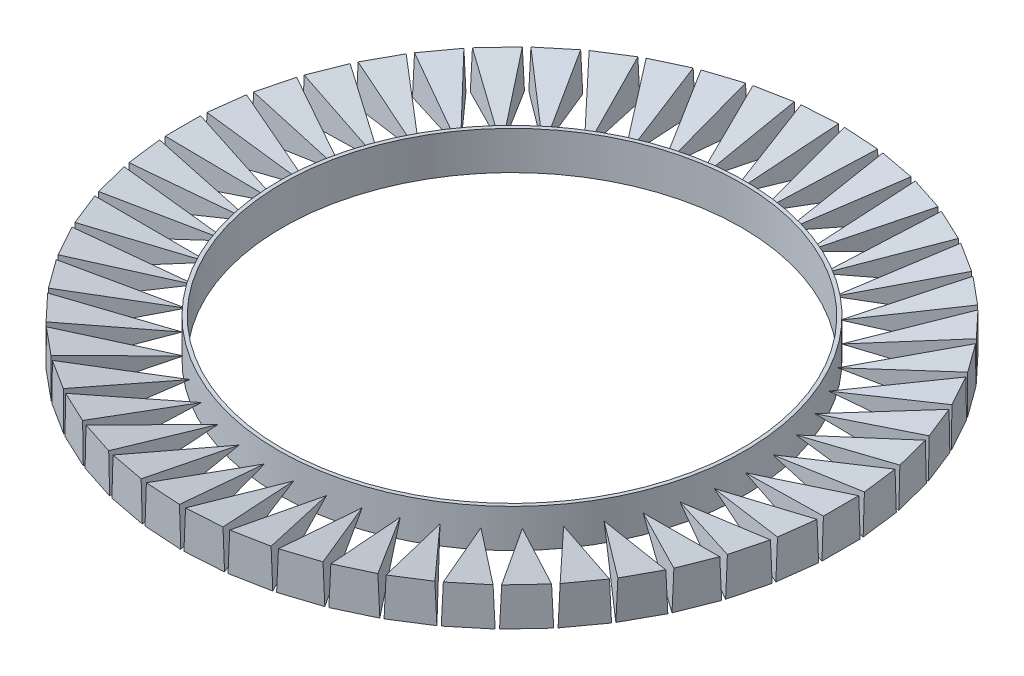
SolidWorks part; units mm, degrees
ref_plane "Front Plane" through (0, 0, 0) normal (0, 0, 1) x (1, 0, 0)
ref_plane "Top Plane" through (0, 0, 0) normal (0, 1, 0) x (1, 0, 0)
ref_plane "Right Plane" through (0, 0, 0) normal (1, 0, 0) x (0, 0, -1)
sketch "Sketch1" plane through (0, 0, 0) normal (1, 0, 0) x (0, 0, -1)
  line L1 (0, 0) -> (10, 0)
  line L2 (0, 0) -> (0, -10)
  line L3 (0, -10) -> (10, -10)
  line L4 (10, 0) -> (10, -10)
  dimension "D1" = 10
  dimension "D2" = 10
  dimension "D3" = 0
  dimension "D4" = 0
extrude "Boss-Extrude1" add sketch "Sketch1" along normal blind 25
sketch "Sketch2" plane through (0, 0, 0) normal (0, 0, 1) x (1, 0, 0)
  line L0 (25, -5) -> (0, 0)
  line L2 (25, 0) -> (25, -10) construction
  line L3 (0, 0) -> (25, 0)
  line L4 (25, 0) -> (25, -5)
extrude "Cut-Extrude1" cut sketch "Sketch2" against normal up to surface (10 mm away) up to face at (12.5, -5, -10)
sketch "Sketch3" plane through (0, 0, 0) normal (0, 0, 1) x (1, 0, 0)
  line L0 (25, -5) -> (0, -10)
  line L1 (0, -10) -> (25, -10)
  line L2 (25, -10) -> (25, -5)
extrude "Cut-Extrude2" cut sketch "Sketch3" against normal up to surface (10 mm away) up to face at (12.5, -6.25, -10)
sketch "Sketch4" plane through (1.9231, -9.6154, 0) normal (0.1961, -0.9806, 0) x (0.9806, 0.1961, 0)
  line L0 (23.5339, -5) -> (-1.9612, 0)
  line L1 (23.5339, -10) -> (23.5339, 0) construction
  line L2 (-1.9612, 0) -> (23.5339, 0)
  line L3 (23.5339, 0) -> (23.5339, -5)
extrude "Cut-Extrude3" cut sketch "Sketch4" against normal up to surface up to face at (12.5, -2.5, -5)
sketch "Sketch5" plane through (1.9231, -9.6154, 0) normal (0.1961, -0.9806, 0) x (0.9806, 0.1961, 0)
  line L0 (23.5339, -5) -> (-1.9612, -10)
  line L1 (-1.9612, -10) -> (23.5339, -10)
  line L2 (23.5339, -10) -> (23.5339, -5)
extrude "Cut-Extrude4" cut sketch "Sketch5" against normal up to surface (10.623 mm away)
pattern_linear "LPattern4" [suppressed] count 10 spacing 10 count 10 spacing 10
sketch "Sketch7" plane through (0, 0, 0) normal (0, 1, 0) x (1, 0, 0)
  circle A0 centre (85.9664, 5) radius 60.9664
  circle A1 centre (85.9664, 5) radius 60
extrude "Boss-Extrude4" add sketch "Sketch7" against normal blind 10 separate body
pattern_circular "CirPattern7" count 50 over 360 about axis through (85.9664, 0, -5) along (0, 1, 0) of bodies 105
